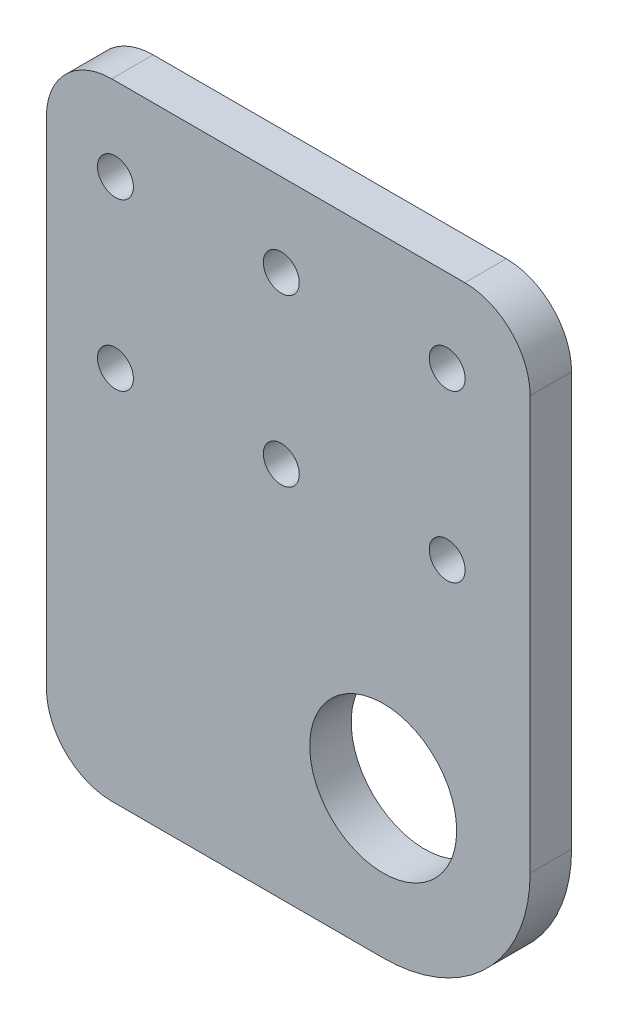
SolidWorks part; units mm, degrees
material "6061-T6 (SS)"
ref_plane "Front" through (0, 0, 0) normal (0, 0, 1) x (1, 0, 0)
ref_plane "Top" through (0, 0, 0) normal (0, 1, 0) x (1, 0, 0)
ref_plane "Right" through (0, 0, 0) normal (1, 0, 0) x (0, 0, -1)
sketch "Sketch1" plane through (0, 0, 0) normal (0, 0, 1) x (1, 0, 0)
  line L0 (-37.035, 25.4) -> (-39.165, 25.4) construction
  line L1 (37.035, -25.4) -> (-37.035, -25.4)
  line L2 (37.035, -25.4) -> (37.035, 25.4)
  line L3 (37.035, 25.4) -> (-37.035, 25.4)
  line L4 (-37.035, -25.4) -> (-37.035, 25.4)
  line L5 (37.035, -25.4) -> (-37.035, 25.4) construction
  line L6 (37.035, 25.4) -> (-37.035, -25.4) construction
  line L7 (-39.165, 25.4) -> (-39.165, -25.4) construction
  line L8 (-39.165, -25.4) -> (-37.035, -25.4) construction
  line L9 (-13.765, 25.4) -> (-13.765, -25.4) construction
  line L10 (-13.765, 0) -> (-39.165, 0) construction
  line L11 (-26.465, 0) -> (-26.465, 25.4) construction
  line L12 (24.335, 25.4) -> (24.335, -25.4) construction
  line L13 (-1.065, 25.4) -> (-1.065, -25.4) construction
  line L14 (-26.465, 12.7) -> (37.035, 12.7) construction
  line L15 (-26.465, -12.7) -> (37.035, -12.7) construction
  circle A0 centre (-26.465, 12.7) radius 2.5 construction
  circle A1 centre (-26.465, -12.7) radius 2.5 construction
  circle A2 centre (-1.065, 12.7) radius 2.5 construction
  circle A3 centre (24.335, 12.7) radius 2.5 construction
  circle A4 centre (24.335, -12.7) radius 2.5 construction
  circle A5 centre (-1.065, -12.7) radius 2.5 construction
  point P0 (0, 0)
  dimension "D5" = 5
  dimension "D8" = 5
  dimension "D1" = 2.13
  dimension "D2" = 25.4
  dimension "D3" = 50.8
  dimension "D4" = 76.2
  dimension "D6" = 12.7
  dimension "D7" = 25.4
extrude "Boss-Extrude1" add sketch "Sketch1" along normal blind 6.35
fillet "Fillet1" radius 10 4 edges at (-37.035, -25.4, 3.175) (37.035, -25.4, 3.175) (37.035, 25.4, 3.175) (-37.035, 25.4, 3.175)
hole_wizard "M5 Clearance Hole1" positions "Sketch3" profile "Sketch2" hole size "M5" standard "ISO" end condition through all
sketch "Sketch3" plane through (0, 0, 6.35) normal (0, 0, 1) x (1, 0, 0)
  point P0 (-26.465, 12.7)
  point P3 (-26.465, -12.7)
  point P6 (-1.065, -12.7)
  point P9 (-1.065, 12.7)
  point P12 (24.335, 12.7)
  point P15 (24.335, -12.7)
sketch "Sketch2" plane through (-26.465, 12.7, 6.35) normal (1, 0, 0) x (0, -1, 0)
  line L0 (0, 0) -> (0, 6.35)
  line L1 (0, 6.35) -> (2.75, 6.35)
  line L2 (2.75, 6.35) -> (2.75, 0)
  line L5 (2.75, 0) -> (0, 0)
  line L11 (0, -6.35) -> (0, 107.95) construction
  dimension "Thru Hole Dia." = 5.5
  dimension "Thru Hole Depth" = 6.35
sketch "Sketch4" plane through (0, 0, 6.35) normal (0, 0, 1) x (1, 0, 0)
  line L0 (37.035, -15.4) -> (37.035, -70.4)
  line L1 (37.035, -70.4) -> (-37.035, -70.4)
  line L2 (-37.035, -70.4) -> (-37.035, -15.4)
  line L3 (-27.035, -25.4) -> (27.035, -25.4) construction
  line L4 (-37.035, -15.4) -> (-27.035, -25.4)
  line L5 (-27.035, -25.4) -> (27.035, -25.4)
  line L6 (27.035, -25.4) -> (37.035, -15.4)
  circle A0 centre (14.535, -47.9) radius 22.5 construction
  dimension "D1" = 45
extrude "Boss-Extrude2" add sketch "Sketch4" against normal blind 6.35
sketch "Sketch5" plane through (0, 0, 6.35) normal (0, 0, 1) x (1, 0, 0)
  circle A0 centre (14.535, -47.9) radius 11.25
  dimension "D1" = 22.5
extrude "Cut-Extrude1" cut sketch "Sketch5" against normal through all
fillet "Fillet2" radius 10 1 edges at (-37.035, -70.4, 3.175)
fillet "Fillet3" radius 22.5 1 edges at (37.035, -70.4, 3.175)
